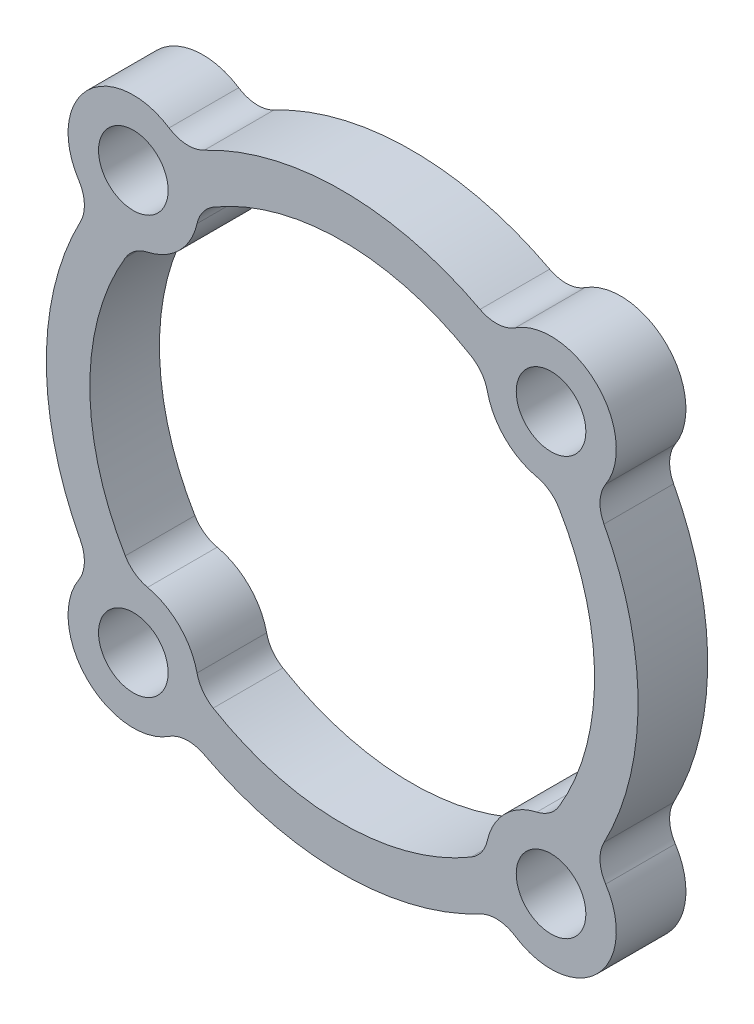
SolidWorks part; units mm, degrees
ref_plane "Plan de face" through (0, 0, 0) normal (0, 0, 1) x (1, 0, 0)
ref_plane "Plan de dessus" through (0, 0, 0) normal (0, 1, 0) x (1, 0, 0)
ref_plane "Plan de droite" through (0, 0, 0) normal (1, 0, 0) x (0, 0, -1)
sketch "Esquisse2" plane through (0, 0, 0) normal (0, 0, 1) x (1, 0, 0)
  circle A0 centre (-12, 12) radius 3.75
  circle A1 centre (12, 12) radius 3.75
  circle A2 centre (-12, -12) radius 3.75
  circle A3 centre (12, -12) radius 3.75
  dimension "D5" = 7.5
  dimension "D1" = 24
  dimension "D2" = 24
  dimension "D3" = 12
  dimension "D4" = 12
extrude "Boss.-Extru.1" add sketch "Esquisse2" along normal blind 4
sketch "Esquisse3" plane through (0, 0, 0) normal (0, 0, 1) x (1, 0, 0)
  circle A0 centre (0, 0) radius 14.5
  circle A1 centre (0, 0) radius 17
  dimension "D1" = 29
  dimension "D2" = 34
extrude "Boss.-Extru.2" add sketch "Esquisse3" along normal blind 4
fillet "Congé1" radius 2 8 edges at (14.3655, 9.0902, 2) (9.0902, 14.3655, 2) (9.0902, -14.3655, 2) (14.3655, -9.0902, 2) (-14.3655, -9.0902, 2) (-9.0902, -14.3655, 2) (-14.3655, 9.0902, 2) (-9.0902, 14.3655, 2)
fillet "Congé2" radius 2 8 edges at (8.2508, -11.9237, 2) (11.9237, -8.2508, 2) (11.9237, 8.2508, 2) (8.2508, 11.9237, 2) (-11.9237, -8.2508, 2) (-8.2508, -11.9237, 2) (-11.9237, 8.2508, 2) (-8.2508, 11.9237, 2)
hole_wizard "Perçage1" positions "Esquisse4" profile "Esquisse5" legacy
sketch "Esquisse4" plane through (0, 0, 0) normal (0, 0, -1) x (-1, 0, 0)
  point P0 (-12, 12)
  point P3 (12, 12)
  point P6 (12, -12)
  point P9 (-12, -12)
sketch "Esquisse5" plane through (12, 12, 0) normal (1, 0, 0) x (0, 1, 0)
  line L0 (0, 0) -> (0, 93.98)
  line L1 (0, 93.98) -> (2, 93.98)
  line L2 (2, 93.98) -> (2, 0)
  line L3 (2, 0) -> (0, 0)
  line L4 (0, 110) -> (0, -10) construction
  dimension "Diamètre" = 4
  dimension "Profondeur" = 93.98
equation "\"D2@Esquisse2\"=\"D1@Esquisse2\""
equation "\"D3@Esquisse2\"=\"D1@Esquisse2\"/2"
equation "\"D4@Esquisse2\"=\"D3@Esquisse2\""
